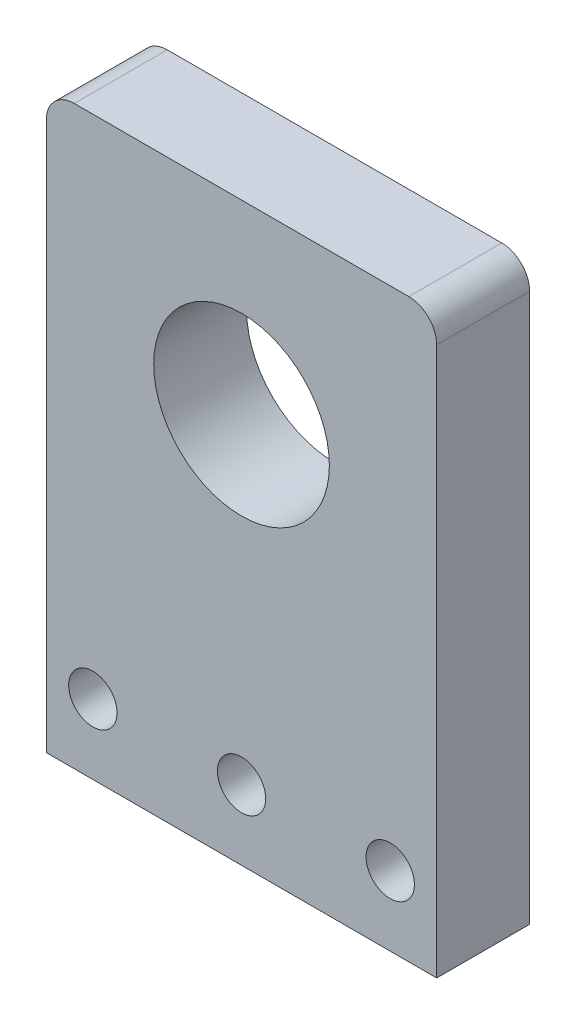
SolidWorks part; units mm, degrees
ref_plane "Front Plane" through (0, 0, 0) normal (0, 0, 1) x (1, 0, 0)
ref_plane "Top Plane" through (0, 0, 0) normal (0, 1, 0) x (1, 0, 0)
ref_plane "Right Plane" through (0, 0, 0) normal (1, 0, 0) x (0, 0, -1)
sketch "Sketch1" plane through (0, 0, 0) normal (0, 0, 1) x (1, 0, 0)
  line L1 (0, 0) -> (42, 0)
  line L2 (0, 0) -> (0, 62)
  line L3 (0, 62) -> (42, 62)
  line L4 (42, 0) -> (42, 62)
  circle A0 centre (21, 42) radius 4.15
  dimension "D3" = 8.3
  dimension "D1" = 42
  dimension "D2" = 62
  dimension "D4" = 20
extrude "Boss-Extrude1" add sketch "Sketch1" along normal blind 10
fillet "Fillet1" radius 3 2 edges at (42, 62, 5) (0, 62, 5)
sketch "Sketch2" plane through (0, 0, 10) normal (0, 0, 1) x (1, 0, 0)
  line L0 (0, 59) -> (0, 0) construction
  line L1 (42, 0) -> (42, 59) construction
  line L2 (0, 0) -> (42, 0) construction
  circle A0 centre (5, 7.5) radius 2.6
  circle A1 centre (21, 7.5) radius 2.6
  circle A2 centre (37, 7.5) radius 2.6
  dimension "D1" = 5.2
  dimension "D2" = 5.2
  dimension "D3" = 5.2
  dimension "D5" = 5
  dimension "D6" = 16
  dimension "D8" = 7.5
  dimension "D9" = 7.5
  dimension "D4" = 5
  dimension "D7" = 7.5
extrude "Cut-Extrude1" cut sketch "Sketch2" against normal through all
sketch "Sketch3" plane through (0, 0, 10) normal (0, 0, 1) x (1, 0, 0)
  circle A0 centre (21, 42) radius 9.45
  dimension "D1" = 18.9
extrude "Cut-Extrude2" cut sketch "Sketch3" against normal blind 10
